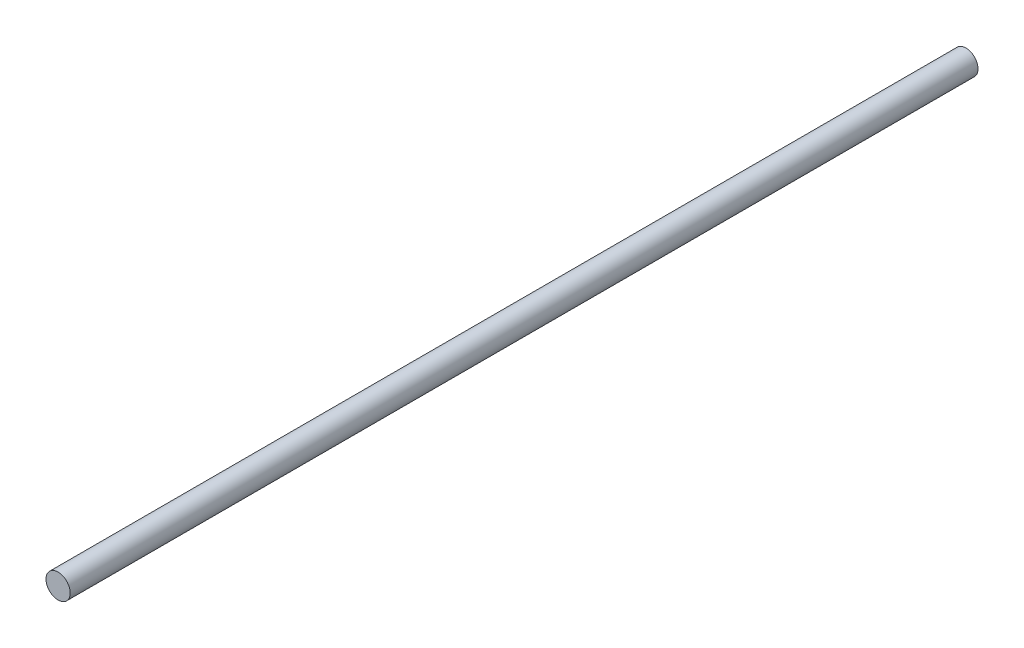
SolidWorks part; units mm, degrees
ref_plane "Front Plane" through (0, 0, 0) normal (0, 0, 1) x (1, 0, 0)
ref_plane "Top Plane" through (0, 0, 0) normal (0, 1, 0) x (1, 0, 0)
ref_plane "Right Plane" through (0, 0, 0) normal (1, 0, 0) x (0, 0, -1)
sketch "Sketch1" plane through (0, 0, 0) normal (0, 0, 1) x (1, 0, 0)
  circle A0 centre (0, 0) radius 4
  dimension "D1" = 8
extrude "Boss-Extrude1" add sketch "Sketch1" along normal blind 300
